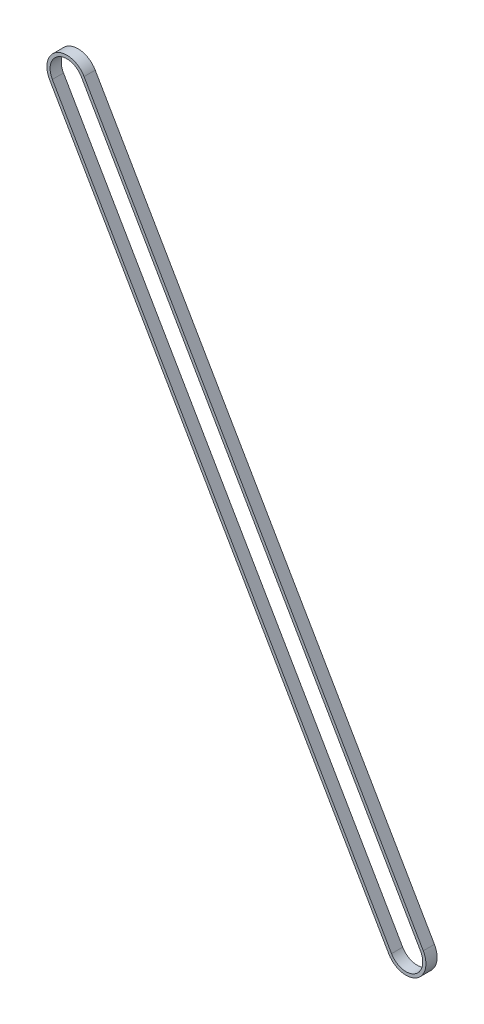
SolidWorks part; units mm, degrees
ref_plane "Front Plane" through (0, 0, 0) normal (0, 0, 1) x (1, 0, 0)
ref_plane "Top Plane" through (0, 0, 0) normal (0, 1, 0) x (1, 0, 0)
ref_plane "Right Plane" through (0, 0, 0) normal (1, 0, 0) x (0, 0, -1)
sketch "Sketch2" plane through (0, 0, 0) normal (0, 0, 1) x (1, 0, 0)
  line L0 (0, 0) -> (1, 0) construction
  line L1 (0, 0) -> (0, 1) construction
  line L2 (-9.0933, -5.25) -> (-221.9433, 363.417)
  line L3 (-203.7567, 373.917) -> (9.0933, 5.25)
  arc A0 (9.0933, 5.25) -> (-9.0933, -5.25) centre (0, 0) cw
  arc A1 (-221.9433, 363.417) -> (-203.7567, 373.917) centre (-212.85, 368.667) cw
extrude "Extrude-Thin1" add sketch "Sketch2" along normal blind 7 thin thin type one direction wall 2
